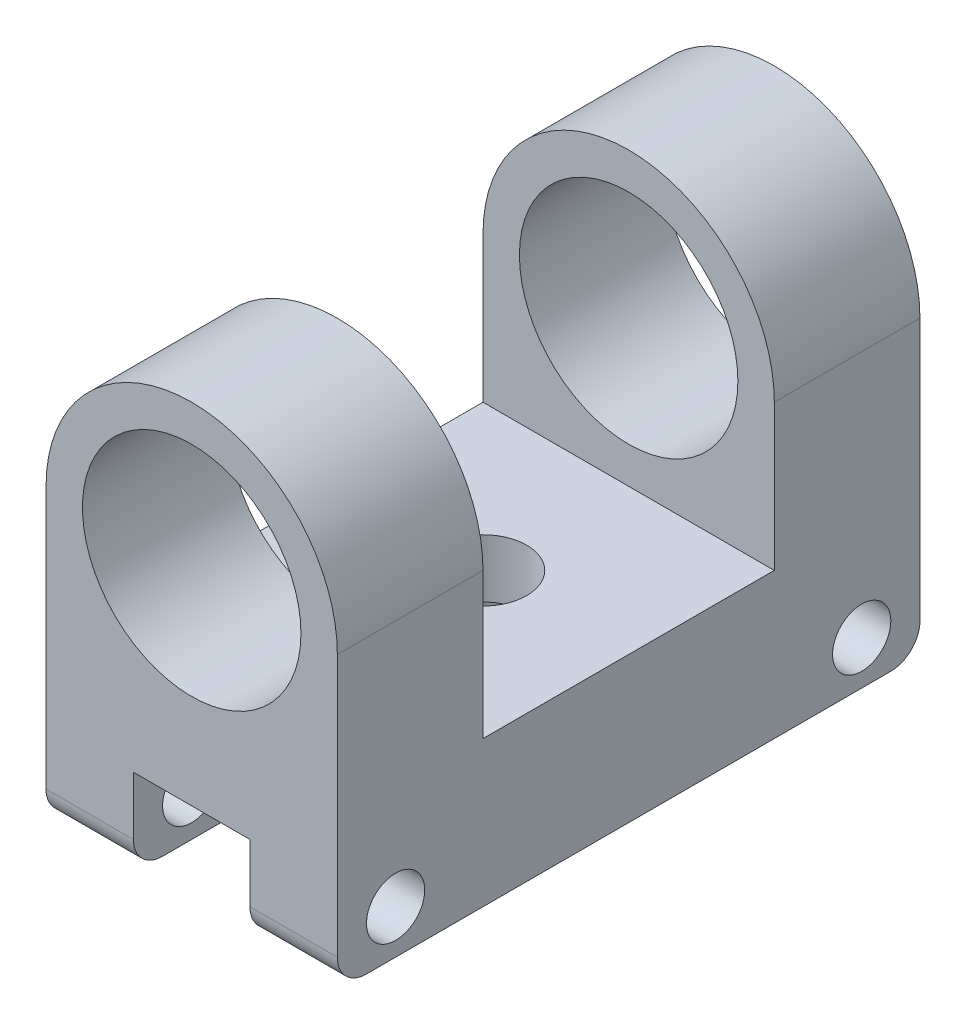
SolidWorks part; units mm, degrees
ref_plane "Front Plane" through (0, 0, 0) normal (0, 0, 1) x (1, 0, 0)
ref_plane "Top Plane" through (0, 0, 0) normal (0, 1, 0) x (1, 0, 0)
ref_plane "Right Plane" through (0, 0, 0) normal (1, 0, 0) x (0, 0, -1)
sketch "Sketch1" plane through (0, 0, 0) normal (0, 0, 1) x (1, 0, 0)
  line L1 (0, 0) -> (100, 0)
  line L2 (0, 0) -> (0, 100)
  line L4 (100, 0) -> (100, 100)
  arc A0 (100, 100) -> (0, 100) centre (50, 100) ccw
  point P6 (0, 0)
  point P7 (0, 0)
  dimension "D1" = 100
  dimension "D2" = 100
extrude "Boss-Extrude1" add sketch "Sketch1" against normal blind 200
sketch "Sketch2" plane through (0, 0, 0) normal (0, 0, 1) x (1, 0, 0)
  line L1 (30, 0) -> (70, 0)
  line L2 (30, 0) -> (30, 30)
  line L3 (0, 100) -> (0, 0)
  line L4 (0, 0) -> (100, 0)
  line L5 (100, 0) -> (100, 100)
  line L6 (0, 100) -> (0, 0)
  line L7 (0, 0) -> (100, 0)
  line L8 (100, 0) -> (100, 100)
  line L9 (30, 30) -> (70, 30)
  line L10 (70, 0) -> (70, 30)
  circle A0 centre (50, 100) radius 37.5
  arc A1 (100, 100) -> (0, 100) centre (50, 100) ccw
  arc A2 (100, 100) -> (0, 100) centre (50, 100) ccw
  line M11 (0, 0) -> (100, 0)
  dimension "D2" = 30
  dimension "D3" = 40
  dimension "D4" = 75
  dimension "D1" = 0
extrude "Cut-Extrude1" cut sketch "Sketch2" against normal blind 200 contours A0 | L10 L9 L2 M11
sketch "Sketch3" plane through (100, 0, 0) normal (1, 0, 0) x (0, 0, -1)
  line L0 (200, 150) -> (0, 150) construction
  line L1 (50, 150) -> (150, 150)
  line L2 (50, 150) -> (50, 50)
  line L3 (50, 50) -> (150, 50)
  line L4 (150, 150) -> (150, 50)
  circle A0 centre (20, 15) radius 10
  circle A1 centre (180, 15) radius 10
  dimension "D1" = 20
  dimension "D2" = 180
  dimension "D3" = 100
  dimension "D4" = 100
extrude "Cut-Extrude2" cut sketch "Sketch3" against normal blind 200
sketch "Sketch4" plane through (0, 50, 0) normal (0, 1, 0) x (1, 0, 0)
  circle A0 centre (50, 100) radius 15
  dimension "D1" = 30
extrude "Cut-Extrude3" cut sketch "Sketch4" against normal blind 200
fillet "Fillet1" radius 10 4 edges at (15, 0, 0) (85, 0, 0) (15, 0, -200) (85, 0, -200)
